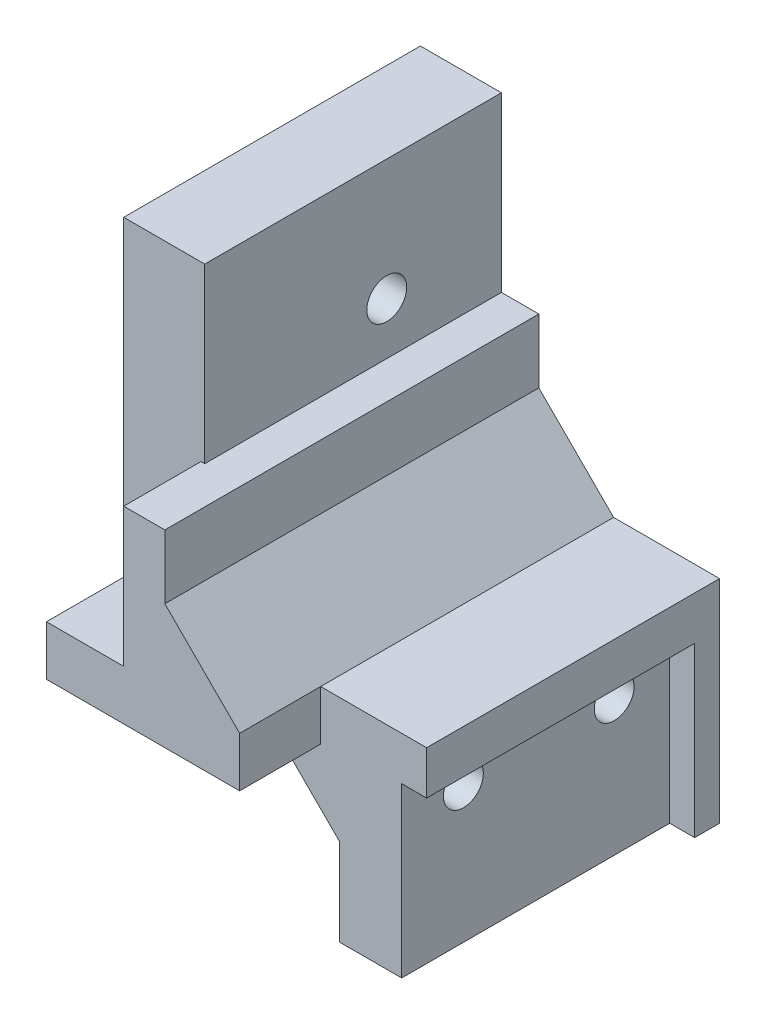
SolidWorks part; units mm, degrees
ref_plane "Alzado" through (0, 0, 0) normal (0, 0, 1) x (1, 0, 0)
ref_plane "Planta" through (0, 0, 0) normal (0, 1, 0) x (1, 0, 0)
ref_plane "Vista lateral" through (0, 0, 0) normal (1, 0, 0) x (0, 0, -1)
sketch "Croquis1" plane through (0, 0, 0) normal (0, 0, 1) x (1, 0, 0)
  line L0 (0, 0) -> (0, -4)
  line L1 (0, -4) -> (11, -4)
  line L2 (11, -4) -> (17, -10)
  line L3 (17, -10) -> (17, -17)
  line L4 (17, -17) -> (24, -17)
  line L5 (24, -17) -> (24, 0)
  line L6 (24, 0) -> (15.5, 0)
  line L7 (6.5, 11.13) -> (6.5, 25)
  line L8 (6.5, 25) -> (0, 25)
  line L9 (0, 25) -> (0, 0)
  line L10 (6.5, 11.13) -> (9.5, 11.13)
  line L11 (9.5, 11.13) -> (9.5, 6)
  line L12 (15.5, 0) -> (9.5, 6)
  dimension "D1" = 24
  dimension "D2" = 7
  dimension "D3" = 4
  dimension "D4" = 25
  dimension "D5" = 6.5
  dimension "D6" = 135
  dimension "D7" = 17
  dimension "D8" = 6
  dimension "D9" = 3
  dimension "D10" = 11.13
  dimension "D11" = 135
  dimension "D12" = 6
extrude "Saliente-Extruir1" add sketch "Croquis1" along normal blind 2
sketch "Croquis5" plane through (0, 0, 2) normal (0, 0, 1) x (1, 0, 0)
  line L0 (22, -17) -> (22, -3.5)
  line L1 (22, -3.5) -> (24, -3.5)
  line L9 (0, 25) -> (0, -4)
  line L10 (0, -4) -> (11, -4)
  line L11 (11, -4) -> (17, -10)
  line L12 (17, -10) -> (17, -17)
  line L13 (17, -17) -> (24, -17)
  line L14 (24, -17) -> (24, 0)
  line L15 (24, 0) -> (15.5, 0)
  line L16 (6.5, 11.13) -> (6.5, 25)
  line L17 (6.5, 25) -> (0, 25)
  line L18 (0, 25) -> (0, -4)
  line L19 (0, -4) -> (11, -4)
  line L20 (11, -4) -> (17, -10)
  line L21 (17, -10) -> (17, -17)
  line L22 (17, -17) -> (22, -17)
  line L23 (24, -3.5) -> (24, 0)
  line L24 (24, 0) -> (15.5, 0)
  line L25 (6.5, 11.13) -> (6.5, 25)
  line L26 (6.5, 25) -> (0, 25)
  line L31 (9.5, 6) -> (9.5, 11.13)
  line L32 (9.5, 6) -> (9.5, 11.13)
  line L33 (9.5, 11.13) -> (6.5, 11.13)
  line L34 (9.5, 11.13) -> (6.5, 11.13)
  line L36 (15.5, 0) -> (9.5, 6)
  line L37 (15.5, 0) -> (9.5, 6)
  dimension "D2" = 13.5
  dimension "D3" = 2
  dimension "D1" = 0
extrude "Saliente-Extruir4" add sketch "Croquis5" along normal blind 28
sketch "Croquis6" plane through (0, 0, 30) normal (0, 0, 1) x (1, 0, 0)
  line L0 (0, 0) -> (6.2, 0)
  line L1 (6.2, 0) -> (6.2, 25)
  line L2 (6.5, 25) -> (0, 25) construction
  line L3 (6.2, 25) -> (0, 25)
  line L4 (0, 25) -> (0, 0)
  dimension "D1" = 6.2
extrude "Cortar-Extruir2" cut sketch "Croquis6" against normal blind 6.2
sketch "Croquis7" plane through (22, 0, 0) normal (1, 0, 0) x (0, 0, -1)
  line L0 (-18.55, -6.05) -> (-6.45, -6.05) construction
  circle A0 centre (-18.55, -6.05) radius 1.6
  circle A1 centre (-6.45, -6.05) radius 1.6
  dimension "D3" = 3.2
  dimension "D1" = 6.05
  dimension "D2" = 11.45
  dimension "D4" = 12.1
extrude "Cortar-Extruir3" cut sketch "Croquis7" against normal up to next
sketch "Croquis8" plane through (0, 0, 23.8) normal (0, 0, 1) x (1, 0, 0)
  line L0 (3.1, 4) -> (3.1, 0) construction
  line L1 (0, 0) -> (6.2, 0) construction
  circle A0 centre (3.1, 4) radius 1.6
  dimension "D1" = 3.2
  dimension "D2" = 4
extrude "Cortar-Extruir4" cut sketch "Croquis8" against normal up to next
sketch "Croquis9" plane through (0, 0, 0) normal (0, 0, -1) x (-1, 0, 0)
  line L1 (-5.95, 2.3546) -> (-3.1, 0.7091)
  line L2 (-3.1, 0.7091) -> (-0.25, 2.3546)
  line L3 (-0.25, 2.3546) -> (-0.25, 5.6454)
  line L4 (-0.25, 5.6454) -> (-3.1, 7.2909)
  line L5 (-3.1, 7.2909) -> (-5.95, 5.6454)
  line L6 (-5.95, 5.6454) -> (-5.95, 2.3546)
  circle A0 centre (-3.1, 4) radius 2.85 construction
  dimension "D1" = 5.7
extrude "Cortar-Extruir5" cut sketch "Croquis9" against normal offset from surface (16.8 mm away) 7 up to face at (4.7, 4, 23.8)
sketch "Croquis10" plane through (17, 0, 0) normal (-1, 0, 0) x (0, 0, 1)
  line L1 (3.1591, -6.05) -> (4.8046, -8.9)
  line L2 (4.8046, -8.9) -> (8.0954, -8.9)
  line L3 (8.0954, -8.9) -> (9.7409, -6.05)
  line L4 (9.7409, -6.05) -> (8.0954, -3.2)
  line L5 (8.0954, -3.2) -> (4.8046, -3.2)
  line L6 (4.8046, -3.2) -> (3.1591, -6.05)
  line L7 (15.2591, -6.05) -> (16.9046, -8.9)
  line L8 (16.9046, -8.9) -> (20.1954, -8.9)
  line L9 (20.1954, -8.9) -> (21.8409, -6.05)
  line L10 (21.8409, -6.05) -> (20.1954, -3.2)
  line L11 (20.1954, -3.2) -> (16.9046, -3.2)
  line L12 (16.9046, -3.2) -> (15.2591, -6.05)
  circle A0 centre (6.45, -6.05) radius 2.85 construction
  circle A1 centre (18.55, -6.05) radius 2.85 construction
  dimension "D1" = 5.7
extrude "Cortar-Extruir6" cut sketch "Croquis10" against normal blind 2.5 and the other way up to next
sketch "Croquis11" plane through (0, 0, 30) normal (0, 0, 1) x (1, 0, 0)
  line L1 (6.2, 25) -> (6.5, 25)
  line L2 (6.2, 25) -> (6.2, 11.13)
  line L3 (6.2, 11.13) -> (6.5, 11.13)
  line L4 (6.5, 25) -> (6.5, 11.13)
extrude "Cortar-Extruir7" cut sketch "Croquis11" against normal up to surface (6.2 mm away) up to face at (4.7, 4, 23.8)
sketch "Croquis12" plane through (6.5, 0, 0) normal (1, 0, 0) x (0, 0, -1)
  line L0 (0, 11.13) -> (0, 25) construction
  line L1 (-23.8, 25) -> (0, 25) construction
  circle A0 centre (-9.2, 15.3) radius 1.6
  dimension "D2" = 3.2
  dimension "D1" = 9.2
  dimension "D3" = 9.7
extrude "Cortar-Extruir8" cut sketch "Croquis12" against normal up to next
sketch "Croquis13" plane through (0, 0, 0) normal (-1, 0, 0) x (0, 0, 1)
  line L1 (9.2, 18.5909) -> (6.35, 16.9454)
  line L2 (6.35, 16.9454) -> (6.35, 13.6546)
  line L3 (6.35, 13.6546) -> (9.2, 12.0091)
  line L4 (9.2, 12.0091) -> (12.05, 13.6546)
  line L5 (12.05, 13.6546) -> (12.05, 16.9454)
  line L6 (12.05, 16.9454) -> (9.2, 18.5909)
  circle A0 centre (9.2, 15.3) radius 2.85 construction
  dimension "D1" = 5.7
extrude "Cortar-Extruir9" cut sketch "Croquis13" against normal blind 3
sketch "Croquis14" plane through (0, 0, 30) normal (0, 0, 1) x (1, 0, 0)
  line L0 (15.5, 0) -> (15.5, -4)
  line L1 (0, -4) -> (11, -4) construction
  line L2 (15.5, -4) -> (11, -4)
  line L14 (9.5, 11.13) -> (6.2, 11.13)
  line L15 (6.2, 11.13) -> (6.2, 0)
  line L16 (6.2, 0) -> (0, 0)
  line L17 (0, 0) -> (0, -4)
  line L18 (0, -4) -> (11, -4)
  line L19 (11, -4) -> (17, -10)
  line L20 (17, -10) -> (17, -17)
  line L21 (17, -17) -> (22, -17)
  line L22 (22, -17) -> (22, -3.5)
  line L23 (22, -3.5) -> (24, -3.5)
  line L24 (24, -3.5) -> (24, 0)
  line L25 (24, 0) -> (15.5, 0)
  line L26 (15.5, 0) -> (9.5, 6)
  line L27 (9.5, 6) -> (9.5, 11.13)
  line L33 (11, -4) -> (17, -10)
  line L34 (17, -10) -> (17, -17)
  line L35 (17, -17) -> (22, -17)
  line L36 (22, -17) -> (22, -3.5)
  line L37 (22, -3.5) -> (24, -3.5)
  line L38 (24, -3.5) -> (24, 0)
  line L39 (24, 0) -> (15.5, 0)
  dimension "D1" = 0
extrude "Cortar-Extruir10" cut sketch "Croquis14" against normal blind 6.5
